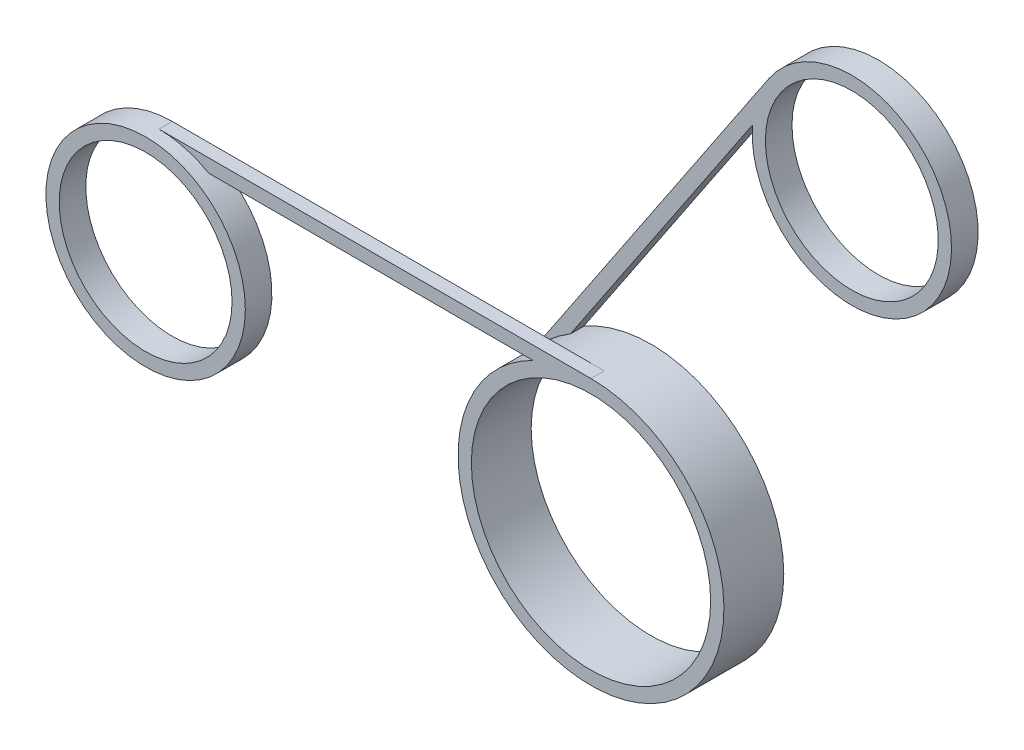
SolidWorks part; units mm, degrees
material "Acciaio al carbonio semplice"
ref_plane "Piano frontale" through (0, 0, 0) normal (0, 0, 1) x (1, 0, 0)
ref_plane "Piano superiore" through (0, 0, 0) normal (0, 1, 0) x (1, 0, 0)
ref_plane "Piano destro" through (0, 0, 0) normal (1, 0, 0) x (0, 0, -1)
sketch "Sketch1" plane through (0, 0, 0) normal (0, 0, 1) x (1, 0, 0)
  circle A0 centre (0, 0) radius 10
  dimension "D2" = 20
extrude "Boss-Extrude1" add sketch "Sketch1" along normal blind 4.5
sketch "Sketch2" plane through (0, 0, 4.5) normal (0, 0, 1) x (1, 0, 0)
  circle A0 centre (0, 0) radius 9
extrude "Cut-Extrude1" cut sketch "Sketch2" against normal blind 4.5
sketch "Sketch3" plane through (0, 0, 4.5) normal (0, 0, 1) x (1, 0, 0)
  line L0 (0, 0) -> (0, 14.6077) construction
  line L1 (0, 0) -> (-18.978, 0) construction
  line L2 (0, 10) -> (-32.5, 10)
  line L3 (0, 9) -> (-32.5, 9)
  line L4 (-32.5, 9) -> (-32.5, 10)
  line L5 (-32.5, 9) -> (-32.5, -3.1529) construction
  line L6 (0, 10) -> (0, 9)
  circle A0 centre (0, 0) radius 10 construction
  circle A1 centre (0, 0) radius 9 construction
  dimension "D1" = 32.5
extrude "Boss-Extrude2" add sketch "Sketch3" against normal blind 1
sketch "Sketch5" plane through (0, 0, 4.5) normal (0, 0, 1) x (1, 0, 0)
  line L0 (-32.5, 10) -> (-32.5, -3.0917) construction
  circle A0 centre (-32.5, 2.5) radius 7.5
extrude "Boss-Extrude3" add sketch "Sketch5" along normal mid plane 2
sketch "Sketch6" plane through (0, 0, 5.5) normal (0, 0, 1) x (1, 0, 0)
  circle A0 centre (-32.5, 2.5) radius 6.5
  circle A1 centre (-32.5, 2.5) radius 7.5 construction
  dimension "D1" = 1
extrude "Cut-Extrude2" cut sketch "Sketch6" against normal blind 2
sketch "Sketch8" plane through (0, 0, 0) normal (0, 0, -1) x (-1, 0, 0)
  line L0 (0, 0) -> (0, 33.0899) construction
  line L1 (0, 10) -> (37.922, 35.3866) construction
  line L3 (0, 10) -> (32.5, 10) construction
  line L4 (8.1941, 5.7321) -> (-9.8855, 32.7391)
  line L5 (-9.8855, 32.7391) -> (-10.7165, 32.1828)
  line L6 (-10.7165, 32.1828) -> (7.3629, 5.1757)
  line L7 (7.3629, 5.1757) -> (8.1941, 5.7321)
  arc A1 (4.3589, 9) -> (0, 10) centre (0, 0) ccw construction
  circle A2 centre (0, 0) radius 10 construction
  circle A3 centre (0, 0) radius 9 construction
  dimension "D1" = 33.8
  dimension "D2" = 90
  dimension "D3" = 32.5
  dimension "D4" = 90
  dimension "D5" = 1
extrude "Boss-Extrude4" add sketch "Sketch8" against normal blind 1
sketch "Sketch9" plane through (0, 0, 0) normal (0, 0, -1) x (-1, 0, 0)
  line L0 (-9.8855, 32.7391) -> (-28.3955, 20.3477) construction
  line L1 (8.1941, 5.7321) -> (-9.8855, 32.7391) construction
  circle A0 centre (-16.1179, 28.5669) radius 7.5
  dimension "D1" = 90
extrude "Boss-Extrude5" add sketch "Sketch9" along normal mid plane 2
sketch "Sketch10" plane through (0, 0, -1) normal (0, 0, -1) x (-1, 0, 0)
  circle A0 centre (-16.1179, 28.5669) radius 6.5
  circle A1 centre (-16.1179, 28.5669) radius 7.5 construction
  dimension "D1" = 1
extrude "Cut-Extrude3" cut sketch "Sketch10" against normal blind 2
sketch "Schizzo1" plane through (0, 0, 0) normal (0, 0, -1) x (-1, 0, 0)
  circle A0 centre (0, 0) radius 9
  circle A1 centre (32.5, 2.5) radius 6.5
  circle A2 centre (-16.1179, 28.5669) radius 6.5
  circle A3 centre (-16.1179, 28.5669) radius 6.5 construction
  circle A4 centre (-16.1179, 28.5669) radius 6.5 construction
  dimension "D1" = 18
  dimension "D2" = 13
  dimension "D3" = 13
  dimension "D4" = 28.5669
  dimension "D5" = 32.5
  dimension "D6" = 2.5
  dimension "D7" = 16.1179
